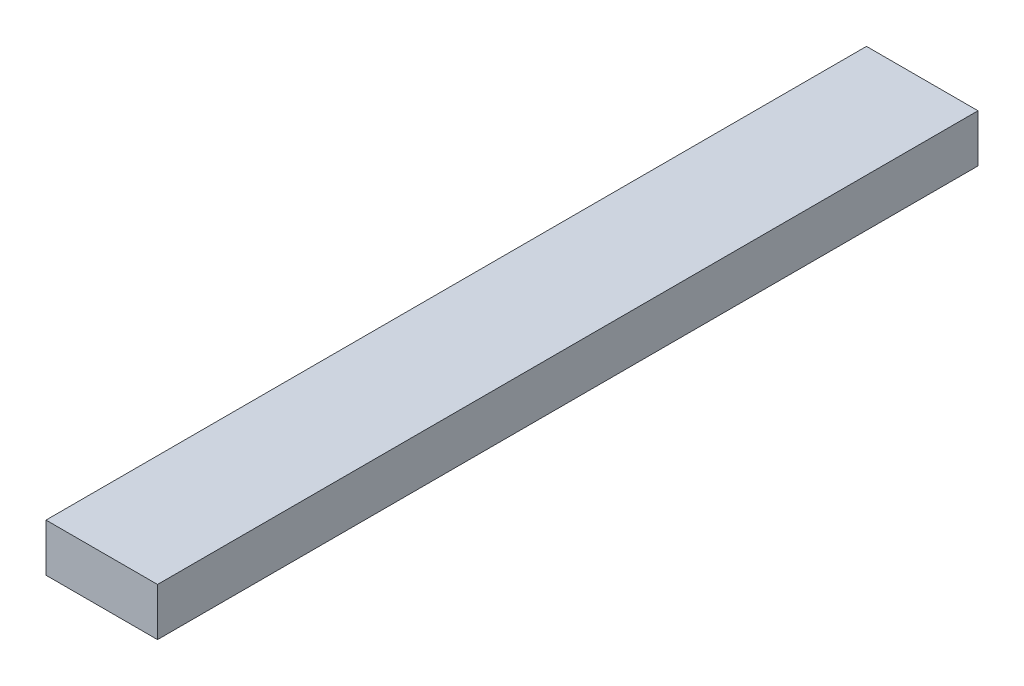
SolidWorks part; units mm, degrees
material "Pine"
ref_plane "Front Plane" through (0, 0, 0) normal (0, 0, 1) x (1, 0, 0)
ref_plane "Top Plane" through (0, 0, 0) normal (0, 1, 0) x (1, 0, 0)
ref_plane "Right Plane" through (0, 0, 0) normal (1, 0, 0) x (0, 0, -1)
sketch "Sketch1" plane through (0, 0, 0) normal (0, 0, 1) x (1, 0, 0)
  line L1 (-73.1682, 74.6988) -> (15.7318, 74.6988)
  line L2 (-73.1682, 74.6988) -> (-73.1682, 36.5988)
  line L3 (-73.1682, 36.5988) -> (15.7318, 36.5988)
  line L4 (15.7318, 74.6988) -> (15.7318, 36.5988)
  dimension "D1" = 38.1
  dimension "D2" = 88.9
extrude "Boss-Extrude1" add sketch "Sketch1" along normal blind 654.05
